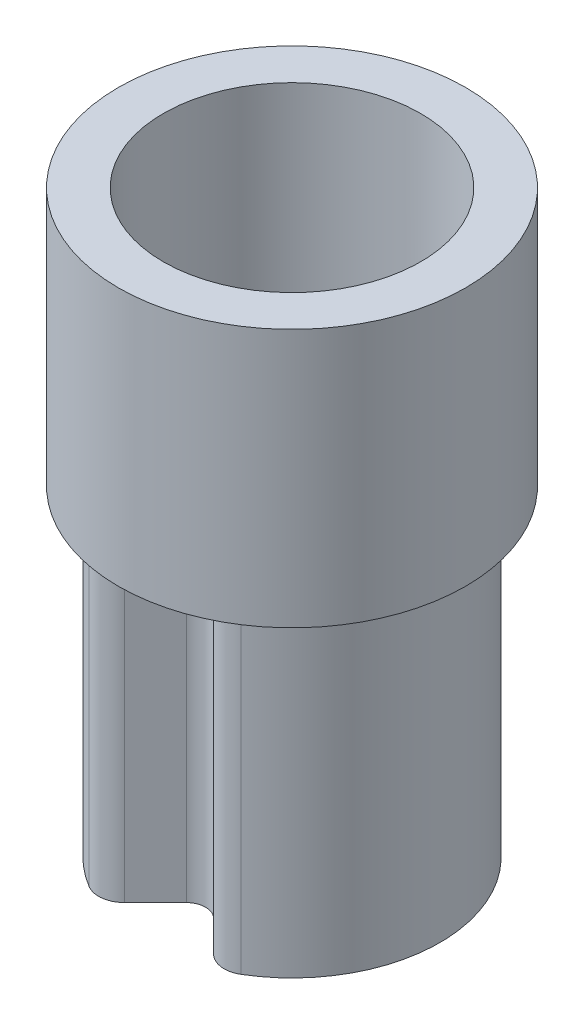
SolidWorks part; units mm, degrees
ref_plane "Front Plane" through (0, 0, 0) normal (0, 0, 1) x (1, 0, 0)
ref_plane "Top Plane" through (0, 0, 0) normal (0, 1, 0) x (1, 0, 0)
ref_plane "Right Plane" through (0, 0, 0) normal (1, 0, 0) x (0, 0, -1)
sketch "Sketch1" plane through (0, 0, 0) normal (0, 1, 0) x (1, 0, 0)
  line L0 (0, 0) -> (0, -1.15) construction
  line L1 (-0.4488, -1.0588) -> (-0.1061, -0.7161)
  line L2 (0.1061, -0.7161) -> (0.4488, -1.0588)
  line L3 (-0.4796, -0.8775) -> (-0.2121, -0.61)
  line L4 (0.2121, -0.61) -> (0.4796, -0.8775)
  arc A0 (0.4488, -1.0588) -> (-0.4488, -1.0588) centre (0, 0) ccw
  arc A1 (0.1061, -0.7161) -> (-0.1061, -0.7161) centre (0, -0.8221) ccw
  arc A2 (0.2121, -0.61) -> (-0.2121, -0.61) centre (0, -0.8221) ccw
  arc A3 (0.4796, -0.8775) -> (-0.4796, -0.8775) centre (0, 0) ccw
  point P8 (0, -0.61)
  dimension "D1" = 2.3
  dimension "D3" = 0.15
  dimension "D2" = 0.61
  dimension "D4" = 0.15
extrude "Boss-Extrude1" add sketch "Sketch1" along normal blind 2.5 contours A3 L3 A2 L4
fillet "Fillet1" radius 0.05 2 edges at (0.4796, 1.25, 0.8775) (-0.4796, 1.25, 0.8775)
fillet "Fillet2" radius 0.2 2 edges at (0.4488, 1.25, 1.0588) (-0.4488, 1.25, 1.0588)
sketch "Sketch2" plane through (0, 2.5, 0) normal (0, 1, 0) x (1, 0, 0)
  circle A0 centre (0, 0) radius 1.35
  circle A1 centre (0, 0) radius 1
  arc A2 (0.5136, -0.858) -> (-0.5136, -0.858) centre (0, 0) ccw construction
  dimension "D1" = 2.7
extrude "Boss-Extrude2" add sketch "Sketch2" along normal offset from surface (2.01 mm away) 4.51 up to face at (0, 0, 0.537)
